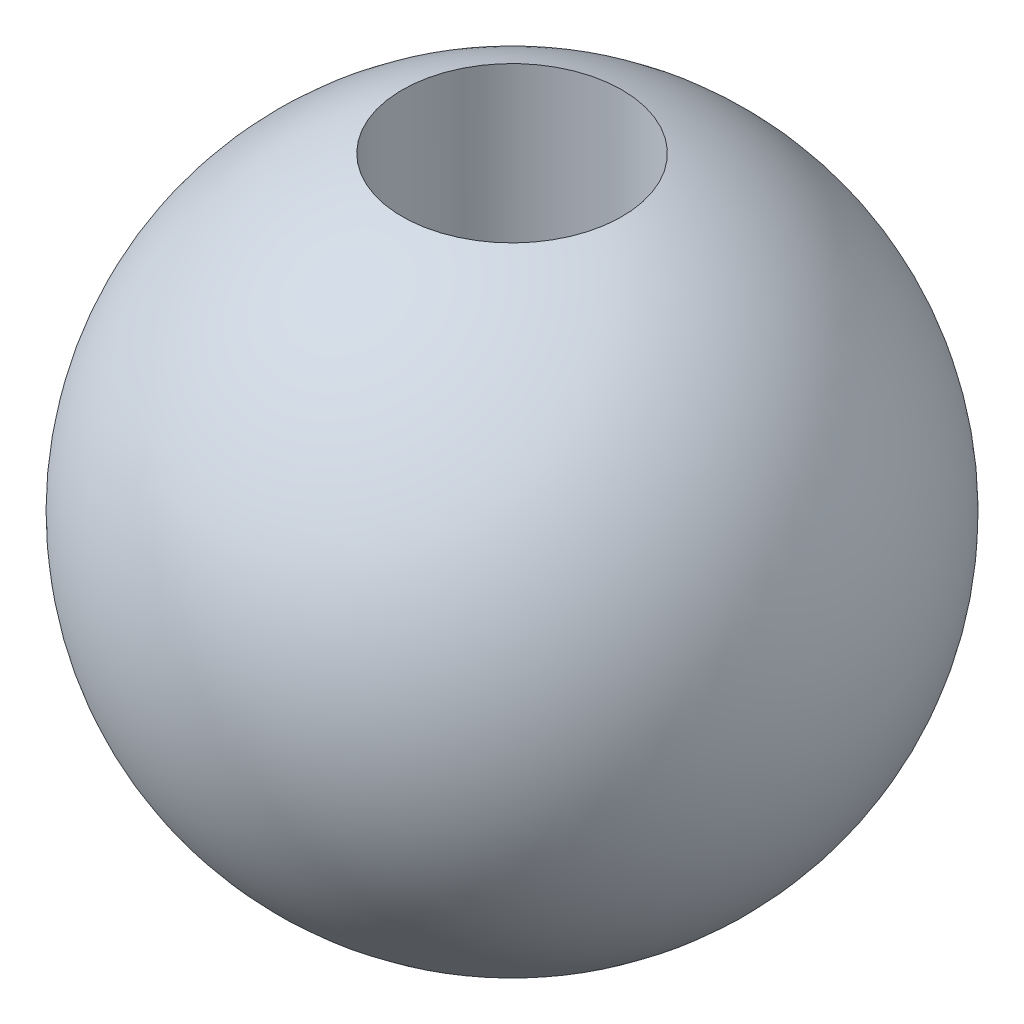
SolidWorks part; units mm, degrees
ref_plane "前视基准面" through (0, 0, 0) normal (0, 0, 1) x (1, 0, 0)
ref_plane "上视基准面" through (0, 0, 0) normal (0, 1, 0) x (1, 0, 0)
ref_plane "右视基准面" through (0, 0, 0) normal (1, 0, 0) x (0, 0, -1)
other "Configuration Table"
sketch "草图1" plane through (0, 0, 0) normal (1, 0, 0) x (0, 0, -1)
  line L0 (0, 3) -> (0, -3)
  arc A0 (0, -3) -> (0, 3) centre (0, 0) ccw
  dimension "D1" = 6
revolve "旋转3" add sketch "草图1" angle 360 about L0
sketch "草图2" plane through (0, 0, 0) normal (0, 1, 0) x (1, 0, 0)
  circle A0 centre (0, 0) radius 1
  dimension "D1" = 2
extrude "切除-拉伸1" cut sketch "草图2" against normal through all both and the other way through all
